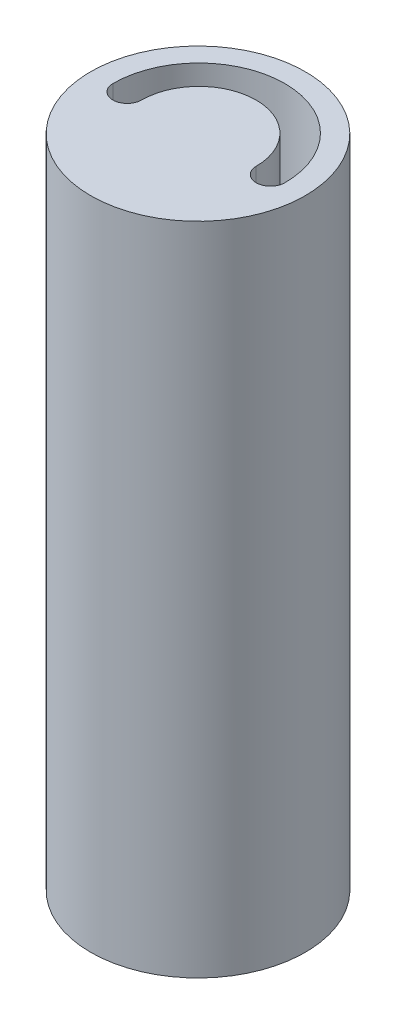
SolidWorks part; units mm, degrees
ref_plane "Front Plane" through (0, 0, 0) normal (0, 0, 1) x (1, 0, 0)
ref_plane "Top Plane" through (0, 0, 0) normal (0, 1, 0) x (1, 0, 0)
ref_plane "Right Plane" through (0, 0, 0) normal (1, 0, 0) x (0, 0, -1)
sketch "Sketch1" plane through (0, 0, 0) normal (0, 0, 1) x (1, 0, 0)
  circle A0 centre (0, 0) radius 28.1
extrude "Boss-Extrude2" add sketch "Sketch1" along normal blind 61.3
sketch "Sketch3" plane through (0, 0, 61.3) normal (0, 0, 1) x (1, 0, 0)
  circle A1 centre (0, -7) radius 18.6
extrude "Cut-Extrude2" cut sketch "Sketch3" against normal blind 58.8 contours A1
sketch "Sketch4" plane through (0, 0, 0) normal (0, 0, -1) x (-1, 0, 0)
  line L1 (-28.1, -28.1) -> (28.1, -28.1)
  line L2 (-28.1, -28.1) -> (-28.1, 28.1)
  line L3 (-28.1, 28.1) -> (28.1, 28.1)
  line L4 (28.1, -28.1) -> (28.1, 28.1)
  line L5 (-28.1, -28.1) -> (28.1, 28.1) construction
  line L6 (-28.1, 28.1) -> (28.1, -28.1) construction
  point P0 (0, 0)
extrude "Boss-Extrude3" add sketch "Sketch4" along normal blind 56.2
sketch "Sketch5" plane through (0, 0, 2.5) normal (0, 0, 1) x (1, 0, 0)
  circle A1 centre (0, -7) radius 16.1
extrude "Cut-Extrude4" cut sketch "Sketch5" against normal blind 5
sketch "Sketch6" plane through (0, 0, -56.2) normal (0, 0, -1) x (-1, 0, 0)
  line L1 (-24.8987, -24.8896) -> (24.8987, -24.8896)
  line L2 (-24.8987, -24.8896) -> (-24.8987, 24.8896)
  line L3 (-24.8987, 24.8896) -> (24.8987, 24.8896)
  line L4 (24.8987, -24.8896) -> (24.8987, 24.8896)
  line L5 (-24.8987, -24.8896) -> (24.8987, 24.8896) construction
  line L6 (-24.8987, 24.8896) -> (24.8987, -24.8896) construction
  point P0 (0, 0)
extrude "Cut-Extrude5" cut sketch "Sketch6" against normal blind 53.7
sketch "Sketch7" plane through (0, -28.1, 0) normal (0, -1, 0) x (-1, 0, 0)
  circle A0 centre (0, 28.1) radius 28.1
extrude "Boss-Extrude4" add sketch "Sketch7" along normal blind 321.5 contours A0
sketch "Sketch8" plane through (0, -349.6, 0) normal (0, -1, 0) x (-1, 0, 0)
  line L1 (-1.6583, 25.8321) -> (1.6583, 25.8321)
  line L3 (-1.6583, 30.8321) -> (1.6583, 30.8321)
  arc A2 (-1.6583, 30.8321) -> (-1.6583, 25.8321) centre (0, 28.3321) ccw
  arc A3 (1.6583, 25.8321) -> (1.6583, 30.8321) centre (0, 28.3321) ccw
extrude "Cut-Extrude6" cut sketch "Sketch8" against normal blind 10
sketch "Sketch9" plane through (0, -349.6, 0) normal (0, -1, 0) x (-1, 0, 0)
  circle A1 centre (0, 28.3321) radius 3
extrude "Cut-Extrude7" cut sketch "Sketch9" against normal blind 1
sketch "Sketch10" plane through (0, -349.6, 0) normal (0, -1, 0) x (-1, 0, 0)
  circle A1 centre (0, 28.3321) radius 6.025
extrude "Cut-Extrude8" cut sketch "Sketch10" against normal blind 0.1
sketch "Sketch15" plane through (0, -349.6, 0) normal (0, -1, 0) x (-1, 0, 0)
  line L0 (6.025, 28.3321) -> (-6.025, 28.3321)
  circle A0 centre (0, 28.3321) radius 6.025 construction
  arc A1 (15, 28.3321) -> (-15, 28.3321) centre (0, 28.3321) ccw
sketch3d "3DSketch2"
  line L1 (-15, -349.6, -28.3321) -> (-22.5, -349.6, -28.3321)
  line L2 (-15, -349.6, -28.3321) -> (-15, -20, -28.3321)
  line L3 (-15, -20, -28.3321) -> (-22.5, -20, -28.3321)
  line L4 (-22.5, -349.6, -28.3321) -> (-22.5, -20, -28.3321)
sweep "Cut-Sweep4" cut profiles "3DSketch2" path "Sketch15"
sketch "Sketch18" plane through (0, 0, 61.3) normal (0, 0, 1) x (1, 0, 0)
  circle A1 centre (0, 18.75) radius 3.75
extrude "Cut-Extrude9" cut sketch "Sketch18" against normal blind 100
sketch "Sketch19" plane through (0, -349.6, 0) normal (0, -1, 0) x (-1, 0, 0)
  circle A0 centre (-18.75, 28.3321) radius 3.75
  circle A1 centre (18.75, 28.3321) radius 3.75
extrude "Cut-Extrude11" cut sketch "Sketch19" against normal blind 325
sketch "Sketch20" plane through (0, 0, -56.2) normal (0, 0, -1) x (-1, 0, 0)
  line L1 (-28.1, -28.1) -> (28.1, -28.1)
  line L2 (-28.1, -28.1) -> (-28.1, 28.1)
  line L3 (-28.1, 28.1) -> (28.1, 28.1)
  line L4 (28.1, -28.1) -> (28.1, 28.1)
extrude "Cut-Extrude13" cut sketch "Sketch20" against normal blind 200
sketch "Sketch21" plane through (0, -28.1, 0) normal (0, 1, 0) x (1, 0, 0)
  circle A1 centre (0, 28.1) radius 28.1
extrude "Cut-Extrude14" cut sketch "Sketch21" against normal blind 150
